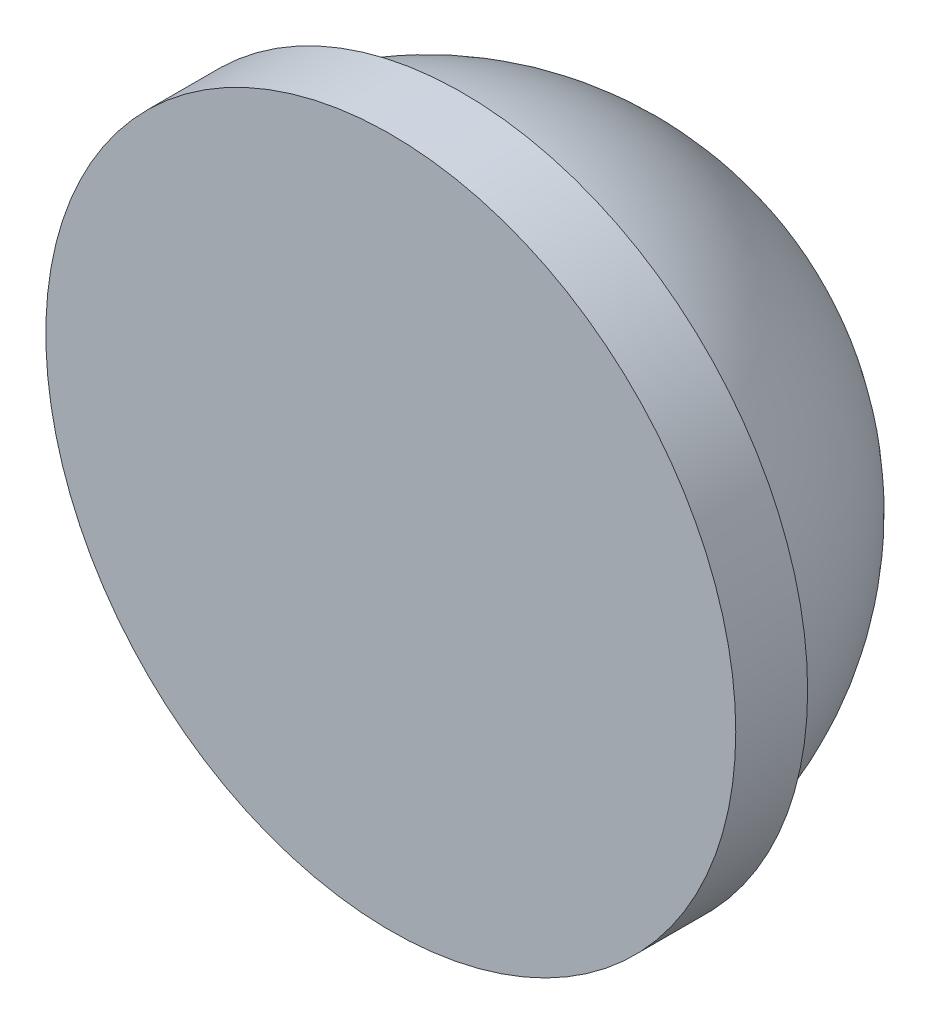
SolidWorks part; units mm, degrees
ref_plane "Plan de face" through (0, 0, 0) normal (0, 0, 1) x (1, 0, 0)
ref_plane "Plan de dessus" through (0, 0, 0) normal (0, 1, 0) x (1, 0, 0)
ref_plane "Plan de droite" through (0, 0, 0) normal (1, 0, 0) x (0, 0, -1)
sketch "Esquisse2" plane through (0, 0, 0) normal (1, 0, 0) x (0, 0, -1)
  line L0 (-0.5, 0) -> (4.5, 0)
  line L3 (0.5, 4.8) -> (-0.5, 4.8)
  line L6 (0.5, 4.8) -> (0, 0) construction
  line L7 (-0.5, 0) -> (-0.5, 4.8)
  line L9 (0, 0) -> (-0.5, 4.8) construction
  line L10 (0.5, 4.4721) -> (0.5, 4.8)
  arc A1 (4.5, 0) -> (0.5, 4.4721) centre (0, 0) ccw
  point P0 (0, 0)
  dimension "D3" = 4.5
  dimension "D1" = 4.8
  dimension "D2" = 1
  dimension "D4" = 5
revolve "Révolution1" add sketch "Esquisse2" angle 360 about L0
